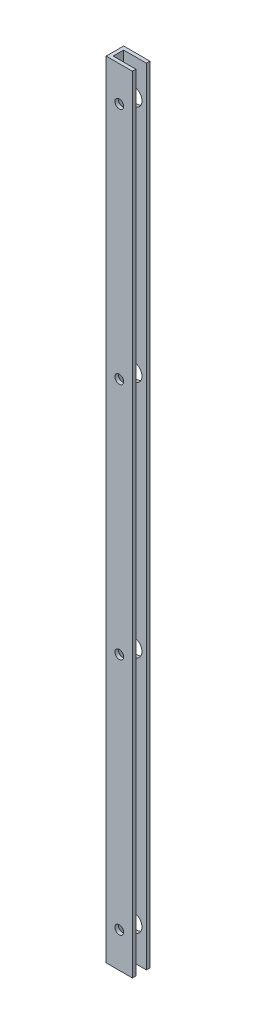
SolidWorks part; units mm, degrees
material "PP Copolymer"
ref_plane "Front Plane" through (0, 0, 0) normal (0, 0, 1) x (1, 0, 0)
ref_plane "Top Plane" through (0, 0, 0) normal (0, 1, 0) x (1, 0, 0)
ref_plane "Right Plane" through (0, 0, 0) normal (1, 0, 0) x (0, 0, -1)
sketch "Sketch1" plane through (0, 0, 0) normal (0, 1, 0) x (1, 0, 0)
  line L0 (19.05, 3.81) -> (19.05, 6.35)
  line L1 (0, -6.35) -> (19.05, -6.35)
  line L2 (0, -6.35) -> (0, 6.35)
  line L3 (0, 6.35) -> (19.05, 6.35)
  line L7 (2.54, -3.81) -> (19.05, -3.81)
  line L8 (2.54, -3.81) -> (2.54, 3.81)
  line L9 (2.54, 3.81) -> (19.05, 3.81)
  line L13 (19.05, -3.81) -> (19.05, -6.35)
  point P0 (0, 0)
  point P1 (2.54, 0)
  point P4 (0, 0)
  point P6 (0, 0)
  dimension "D1" = 2.54
  dimension "D2" = 19.05
  dimension "D3" = 2.54
  dimension "D4" = 12.7
extrude "Boss-Extrude1" add sketch "Sketch1" along normal mid plane 571.5
sketch "Sketch2" plane through (0, 0, 0) normal (-1, 0, 0) x (0, 0, 1)
  line L1 (-6.35, 285.75) -> (6.35, 285.75) construction
  circle A0 centre (-0.2864, 279.4) radius 1.27
  circle A1 centre (-0.2864, 222.25) radius 1.27
  circle A2 centre (-0.2864, 165.1) radius 1.27
  circle A3 centre (-0.2864, 107.95) radius 1.27
  circle A4 centre (-0.2864, 50.8) radius 1.27
  circle A5 centre (-0.2864, -6.35) radius 1.27
  circle A6 centre (-0.2864, -63.5) radius 1.27
  circle A7 centre (-0.2864, -120.65) radius 1.27
  circle A8 centre (-0.2864, -177.8) radius 1.27
  circle A9 centre (-0.2864, -234.95) radius 1.27
  dimension "D1" = 2.54
  dimension "D2" = 6.35
  dimension "D3" = 10
extrude "Cut-Extrude1" cut sketch "Sketch2" against normal through all
sketch "Sketch4" plane through (0, 0, 3.81) normal (0, 0, -1) x (-1, 0, 0)
  line L0 (0, 285.75) -> (-19.05, 285.75) construction
  circle A0 centre (-9.525, 260.35) radius 3.175
  circle A1 centre (-9.525, 86.868) radius 3.175
  circle A2 centre (-9.525, -86.614) radius 3.175
  circle A3 centre (-9.525, -260.096) radius 3.175
  point P5 (-9.525, 285.75)
  dimension "D1" = 6.35
  dimension "D2" = 25.4
  dimension "D3" = 4
extrude "Cut-Extrude2" cut sketch "Sketch4" against normal blind 140.208
sketch "Sketch5" plane through (0, 0, -6.35) normal (0, 0, -1) x (-1, 0, 0)
  line L0 (0, 285.75) -> (-19.05, 285.75) construction
  circle A0 centre (-9.525, 260.35) radius 6.35
  circle A1 centre (-9.525, 86.7918) radius 6.35
  circle A2 centre (-9.525, -86.7664) radius 6.35
  circle A3 centre (-9.525, -260.3246) radius 6.35
  point P5 (-9.525, 285.75)
  dimension "D1" = 12.7
  dimension "D2" = 25.4
  dimension "D3" = 4
extrude "Cut-Extrude3" cut sketch "Sketch5" against normal up to vertex (2.54 mm away)
